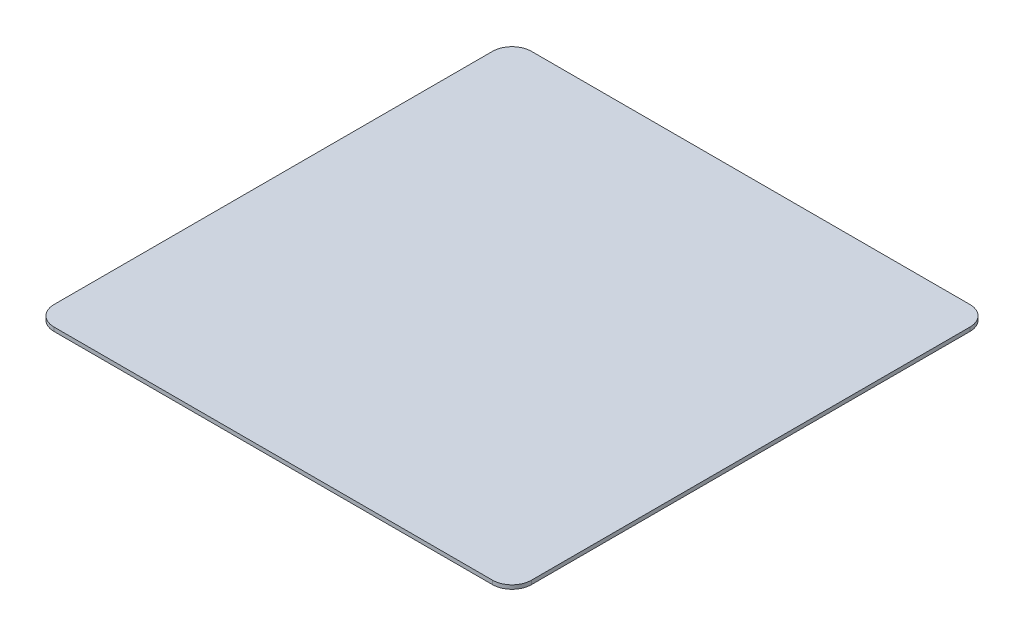
SolidWorks part; units mm, degrees
other "标注2"
sketch "草图3" plane through (-122.5, 2, -122.5) normal (0, 1, 0) x (1, 0, 0)
other "细节项目1"
ref_plane "前视基准面" through (0, 0, 0) normal (0, 0, 1) x (1, 0, 0)
ref_plane "上视基准面" through (0, 0, 0) normal (0, 1, 0) x (1, 0, 0)
ref_plane "右视基准面" through (0, 0, 0) normal (1, 0, 0) x (0, 0, -1)
sketch "草图1" plane through (0, 0, 0) normal (0, 1, 0) x (1, 0, 0)
  line L1 (-122.5, 122.5) -> (122.5, 122.5)
  line L2 (-122.5, 122.5) -> (-122.5, -122.5)
  line L3 (-122.5, -122.5) -> (122.5, -122.5)
  line L4 (122.5, 122.5) -> (122.5, -122.5)
  line L5 (-122.5, 122.5) -> (122.5, -122.5) construction
  line L6 (-122.5, -122.5) -> (122.5, 122.5) construction
  point P1 (0, 0)
  dimension "D1" = 245
  dimension "D2" = 245
extrude "凸台-拉伸1" add sketch "草图1" along normal blind 2
fillet "圆角1" radius 10 4 edges at (-122.5, 1, -122.5) (122.5, 1, -122.5) (-122.5, 1, 122.5) (122.5, 1, 122.5)
